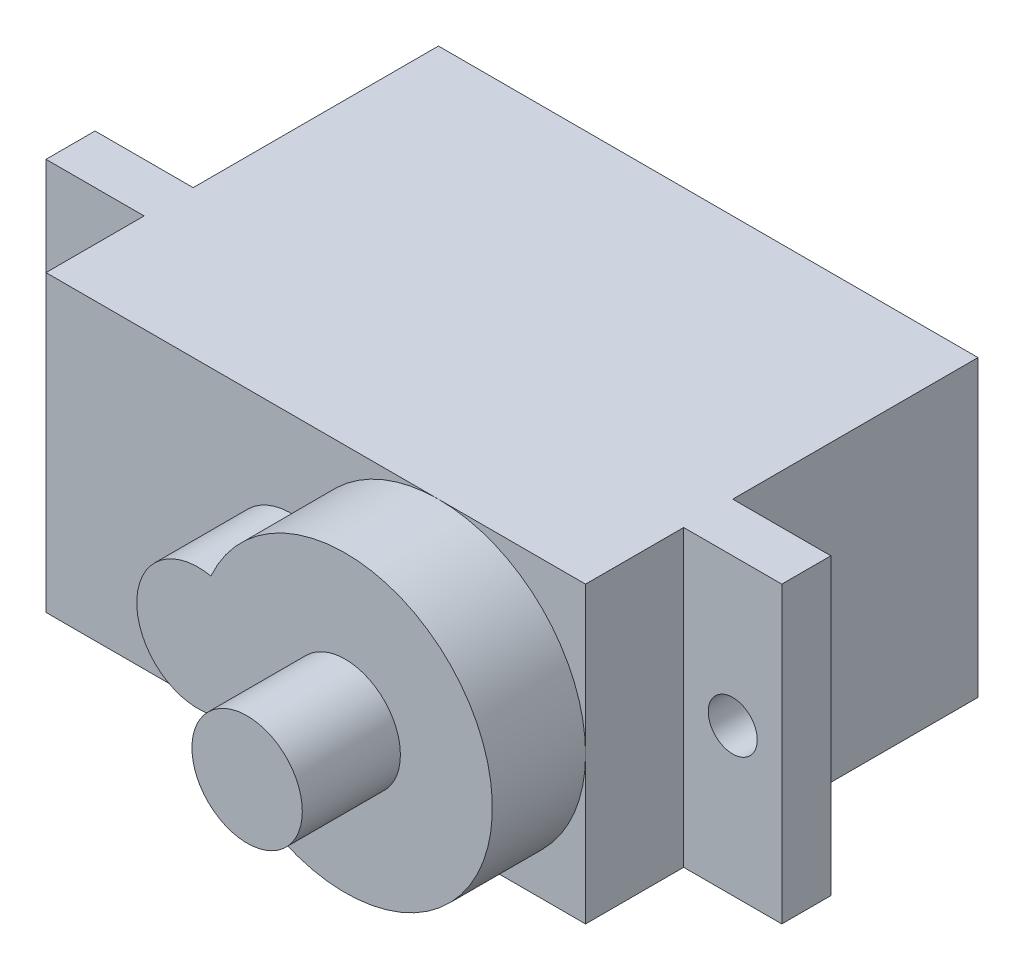
SolidWorks part; units mm, degrees
material "ABS"
ref_plane "前视基准面" through (0, 0, 0) normal (0, 0, 1) x (1, 0, 0)
ref_plane "上视基准面" through (0, 0, 0) normal (0, 1, 0) x (1, 0, 0)
ref_plane "右视基准面" through (0, 0, 0) normal (1, 0, 0) x (0, 0, -1)
sketch "Sketch1" plane through (0, 0, 0) normal (0, 0, 1) x (1, 0, 0)
  line L1 (-11, 6) -> (11, 6)
  line L2 (-11, 6) -> (-11, -6)
  line L3 (-11, -6) -> (11, -6)
  line L4 (11, 6) -> (11, -6)
  dimension "D1" = 12
  dimension "D2" = 22
  dimension "D3" = 6
  dimension "D4" = 11
extrude "Extrude1" add sketch "Sketch1" along normal blind 10
sketch "Sketch2" plane through (0, 0, 10) normal (0, 0, 1) x (1, 0, 0)
  line L1 (-15, 6) -> (15, 6)
  line L2 (-15, 6) -> (-15, -6)
  line L3 (-15, -6) -> (15, -6)
  line L4 (15, 6) -> (15, -6)
  line L6 (11, 6) -> (-11, 6) construction
  line L7 (-11, -6) -> (11, -6) construction
  line L8 (11, -6) -> (11, 6) construction
  line L9 (-11, 6) -> (-11, -6) construction
  dimension "D1" = 4
  dimension "D2" = 4
extrude "Extrude2" add sketch "Sketch2" along normal blind 2
sketch "Sketch3" plane through (0, 0, 12) normal (0, 0, 1) x (1, 0, 0)
  line L1 (-11, 6) -> (11, 6)
  line L2 (-11, 6) -> (-11, -6)
  line L3 (-11, -6) -> (11, -6)
  line L4 (11, 6) -> (11, -6)
extrude "Extrude3" add sketch "Sketch3" along normal blind 4
sketch "Sketch4" plane through (0, 0, 12) normal (0, 0, 1) x (1, 0, 0)
  line L0 (-13.1462, 0) -> (17.5224, 0) construction
  line L1 (11, -6) -> (11, 6) construction
  line L2 (-11, 6) -> (-11, -6) construction
  circle A0 centre (-13, 0) radius 1
  circle A1 centre (13, 0) radius 1
  dimension "D1" = 2
  dimension "D2" = 2
  dimension "D3" = 2
  dimension "D4" = 2
extrude "Extrude4" cut sketch "Sketch4" against normal through all
sketch "Sketch5" plane through (0, 0, 16) normal (0, 0, 1) x (1, 0, 0)
  line L0 (11, -6) -> (11, 6) construction
  line L1 (11, 6) -> (-11, 6) construction
  line L2 (-11, -6) -> (11, -6) construction
  line L3 (11, -6) -> (11, 6) construction
  arc A0 (-0.4792, -2.4451) -> (-0.4792, 2.4451) centre (5, 0) ccw
  arc A1 (-0.4792, 2.4451) -> (-0.4792, -2.4451) centre (-1, 0) ccw
  dimension "D1" = 5
  dimension "D2" = 12
extrude "Extrude5" add sketch "Sketch5" along normal blind 3.8
sketch "Sketch6" plane through (0, 0, 19.8) normal (0, 0, 1) x (1, 0, 0)
  circle A0 centre (5, 0) radius 2.25
  dimension "D1" = 4.5
extrude "Extrude6" add sketch "Sketch6" along normal blind 4
